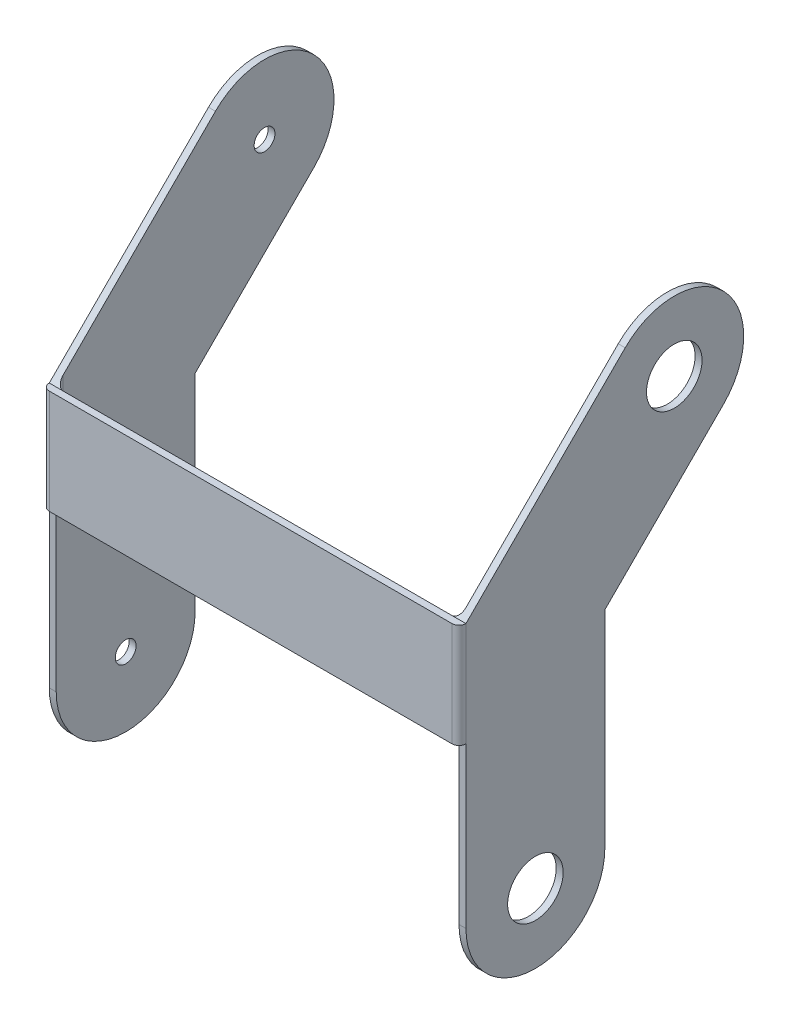
SolidWorks part; units mm, degrees
ref_plane "Front Plane" through (0, 0, 0) normal (0, 0, 1) x (1, 0, 0)
ref_plane "Top Plane" through (0, 0, 0) normal (0, 1, 0) x (1, 0, 0)
ref_plane "Right Plane" through (0, 0, 0) normal (1, 0, 0) x (0, 0, -1)
sketch "Sketch1" plane through (0, 0, 0) normal (1, 0, 0) x (0, 0, -1)
  line L0 (0, 0) -> (22.9286, 22.9286)
  line L1 (37.0708, 8.7865) -> (20, -8.2843)
  line L2 (20, -8.2843) -> (20, -38.019)
  line L3 (0, -38.019) -> (0, 0)
  line L4 (22.9286, 22.9286) -> (37.0708, 8.7865) construction
  arc A0 (22.9286, 22.9286) -> (37.0708, 8.7865) centre (29.9997, 15.8576) cw
  arc A1 (20, -38.019) -> (0, -38.019) centre (10, -38.019) cw
  circle A2 centre (29.9997, 15.8576) radius 1.5
  circle A3 centre (10, -38.019) radius 1.5
  dimension "D1" = 135
  dimension "D2" = 10
  dimension "D3" = 10
  dimension "D6" = 3
  dimension "D7" = 3
  dimension "D4" = 32.426
  dimension "D5" = 38.019
extrude "Boss-Extrude1" add sketch "Sketch1" along normal blind 1
sketch "Sketch2" plane through (1, 0, 0) normal (1, 0, 0) x (0, 0, -1)
  line L1 (0, 0) -> (-1, 0)
  line L2 (0, 0) -> (0, -15)
  line L3 (0, -15) -> (-1, -15)
  line L4 (-1, 0) -> (-1, -15)
  dimension "D1" = 15
  dimension "D2" = 1
extrude "Boss-Extrude2" add sketch "Sketch2" along normal blind 30 from offset 1 offset against normal yes
ref_plane "Plane1" through (30, 0, 0) normal (-1, 0, 0) x (0, 0, 1)
mirror "Mirror2" about plane through (30, 0, 0) normal (-1, 0, 0) of "Boss-Extrude2", "Boss-Extrude1"
fillet "Fillet1" radius 1 4 edges at (1, -7.5, 0) (59, -7.5, 0) (0, -7.5, 1) (60, -7.5, 1)
sketch "Sketch3" plane through (60, 0, 0) normal (1, 0, 0) x (0, 0, -1)
  circle A0 centre (29.9997, 15.8576) radius 4
  circle A1 centre (10, -38.019) radius 4
  dimension "D1" = 8
  dimension "D2" = 8
extrude "Cut-Extrude1" cut sketch "Sketch3" against normal up to next
